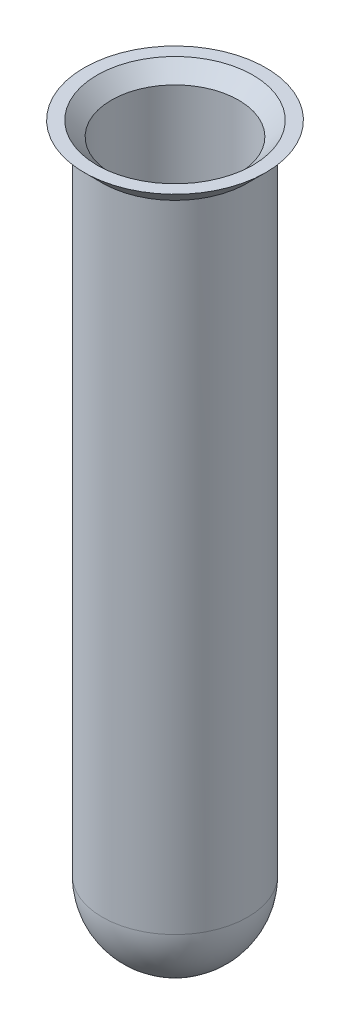
SolidWorks part; units mm, degrees
ref_plane "Plano frontal" through (0, 0, 0) normal (0, 0, 1) x (1, 0, 0)
ref_plane "Plano superior" through (0, 0, 0) normal (0, 1, 0) x (1, 0, 0)
ref_plane "Plano direito" through (0, 0, 0) normal (1, 0, 0) x (0, 0, -1)
sketch "Sketch1" plane through (0, 0, 0) normal (0, 0, 1) x (1, 0, 0)
  line L0 (0, 3.6777) -> (0, -60.3223) construction
  line L1 (0, 3.6777) -> (10, 3.6777)
  line L2 (10, 3.6777) -> (8, 1.6777)
  line L3 (8, 1.6777) -> (8, -68.3223)
  line L4 (0, 3.6777) -> (0, -76.3223)
  line L5 (0, -60.3223) -> (0, -76.3223) construction
  arc A0 (0, -76.3223) -> (8, -68.3223) centre (0, -68.3223) ccw
  dimension "D1" = 8
  dimension "D2" = 80
  dimension "D3" = 2
  dimension "D4" = 10
revolve "Revolve2" add sketch "Sketch1" angle 360 about L4
shell "Shell8" thickness 1
